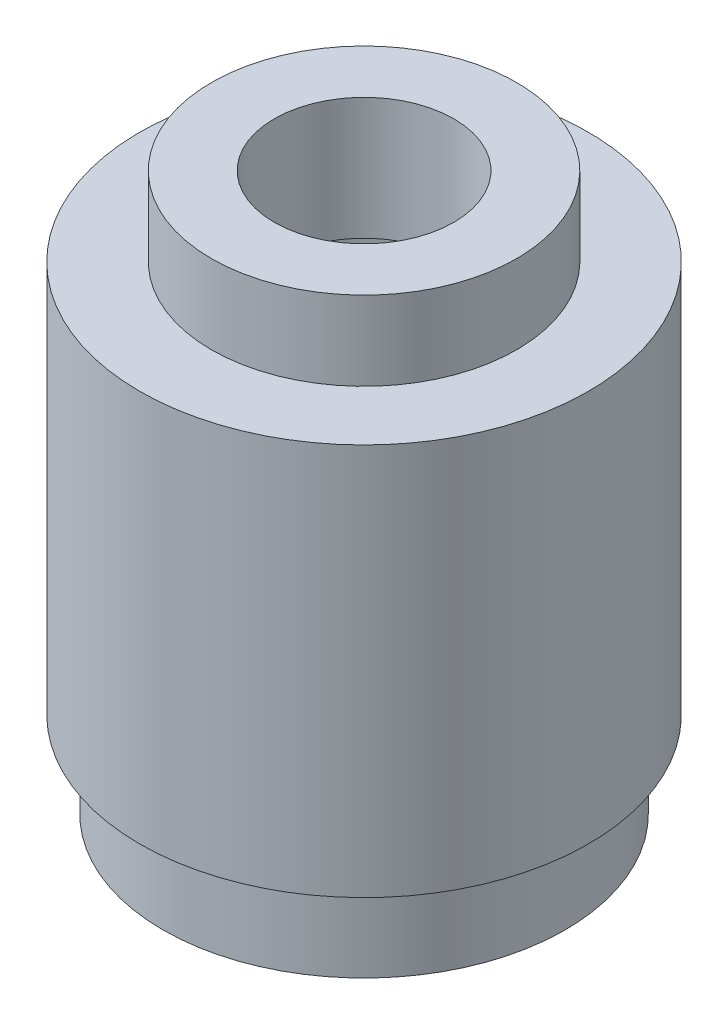
SolidWorks part; units mm, degrees
ref_plane "Front Plane" through (0, 0, 0) normal (0, 0, 1) x (1, 0, 0)
ref_plane "Top Plane" through (0, 0, 0) normal (0, 1, 0) x (1, 0, 0)
ref_plane "Right Plane" through (0, 0, 0) normal (1, 0, 0) x (0, 0, -1)
sketch "Sketch1" plane through (0, 0, 0) normal (0, 0, 1) x (1, 0, 0)
  line L0 (0, 42.2943) -> (0, -46.9331) construction
  line L1 (0, -55) -> (0, 55) construction
  line L2 (2.6988, -4.2291) -> (2.6988, -1.9431)
  line L3 (2.6988, -4.2291) -> (3.556, -4.2291)
  line L4 (3.556, -4.2291) -> (3.556, -2.7051)
  line L5 (3.556, -2.7051) -> (3.9688, -2.7051)
  line L6 (3.9688, -2.7051) -> (3.9688, 4.2291)
  line L7 (3.9688, 4.2291) -> (2.6988, 4.2291)
  line L8 (2.6988, 4.2291) -> (2.6988, 5.6261)
  line L9 (2.6988, 5.6261) -> (1.5875, 5.6261)
  line L10 (1.5875, 5.6261) -> (1.5875, 3.4671)
  line L11 (1.5875, 3.4671) -> (3.4608, 3.4671)
  line L12 (2.6988, -1.9431) -> (3.4608, -1.9431)
  line L13 (3.4608, -1.9431) -> (3.4608, 3.4671)
  line L14 (55, 0) -> (-55, 0) construction
  dimension "D2" = 1.524
  dimension "D3" = 7.9375
  dimension "D4" = 8.4582
  dimension "D5" = 1.397
  dimension "D6" = 5.3975
  dimension "D7" = 4.2291
  dimension "D8" = 3.175
  dimension "D9" = 7.112
  dimension "D10" = 0.762
  dimension "D11" = 5.3975
  dimension "D12" = 0.508
  dimension "D13" = 0.762
revolve "Revolve1" add sketch "Sketch1" angle 360 about L0
